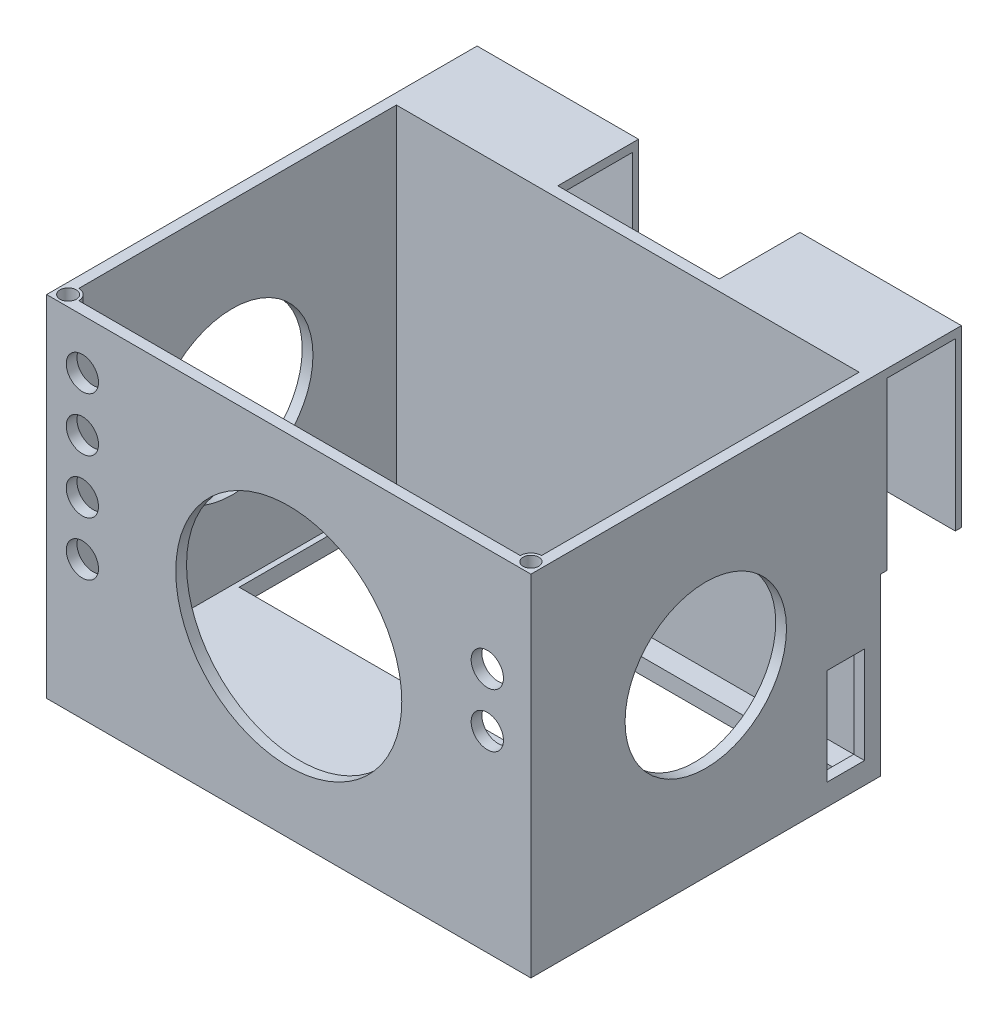
SolidWorks part; units mm, degrees
ref_plane "Front Plane" through (0, 0, 0) normal (0, 0, 1) x (1, 0, 0)
ref_plane "Top Plane" through (0, 0, 0) normal (0, 1, 0) x (1, 0, 0)
ref_plane "Right Plane" through (0, 0, 0) normal (1, 0, 0) x (0, 0, -1)
sketch "Sketch7" plane through (0, 0, 0) normal (0, 1, 0) x (1, 0, 0)
  line L1 (-45, 32.5) -> (45, 32.5)
  line L2 (-45, 32.5) -> (-45, -32.5)
  line L3 (-45, -32.5) -> (45, -32.5)
  line L4 (45, 32.5) -> (45, -32.5)
  line L5 (-45, 32.5) -> (45, -32.5) construction
  line L6 (-45, -32.5) -> (45, 32.5) construction
  line L11 (-42.1497, 30.4415) -> (26.6705, -19.262) construction
  point P0 (0, 0)
  point P6 (0, 0)
  dimension "D1" = 90
  dimension "D2" = 65
extrude "Boss-Extrude2" add sketch "Sketch7" against normal blind 65
sketch "Sketch10" plane through (0, 0, 0) normal (0, 1, 0) x (1, 0, 0)
  line L1 (-43, 30.5) -> (43, 30.5)
  line L2 (-43, 30.5) -> (-43, -30.5)
  line L3 (-43, -30.5) -> (43, -30.5)
  line L4 (43, 30.5) -> (43, -30.5)
  line L5 (-43, 30.5) -> (43, -30.5) construction
  line L6 (-43, -30.5) -> (43, 30.5) construction
  point P0 (0, 0)
  dimension "D1" = 86
  dimension "D2" = 61
extrude "Cut-Extrude2" cut sketch "Sketch10" against normal blind 62
sketch "Sketch12" plane through (-45, 0, 0) normal (-1, 0, 0) x (0, 0, 1)
  circle A0 centre (0, -32.5) radius 15
extrude "Cut-Extrude3" cut sketch "Sketch12" against normal through all
sketch "Sketch13" plane through (0, 0, 32.5) normal (0, 0, 1) x (1, 0, 0)
  circle A0 centre (0, -32.5) radius 21
  circle A1 centre (-38.3562, -9.3091) radius 3
  circle A2 centre (-38.3562, -19.3091) radius 3
  circle A3 centre (-38.3562, -29.3091) radius 3
  circle A4 centre (-38.3562, -39.3091) radius 3
  circle A5 centre (36.897, -19.3091) radius 3
  circle A6 centre (36.897, -29.3091) radius 3
  dimension "D1" = 4
  dimension "D2" = 2
extrude "Cut-Extrude4" cut sketch "Sketch13" against normal up to surface (2 mm away) up to face at (0, -31, 30.5)
sketch "Sketch14" plane through (45, 0, 0) normal (1, 0, 0) x (0, 0, -1)
  line L0 (32.5, -65) -> (32.5, 0) construction
  line L3 (29.5, -61) -> (29.5, -43.0371)
  line L4 (29.5, -43.0371) -> (22.5, -43.0371)
  line L5 (22.5, -43.0371) -> (22.5, -61)
  line L6 (22.5, -61) -> (29.5, -61)
  dimension "D1" = 7
  dimension "D2" = 3
extrude "Cut-Extrude5" cut sketch "Sketch14" against normal blind 5
sketch "Sketch15" plane through (0, -65, 0) normal (0, -1, 0) x (1, 0, 0)
  line L0 (-45, -32.5) -> (-45, 32.5) construction
  line L1 (-42, -0.2844) -> (42, -0.2844)
  line L2 (-42, -0.2844) -> (-42, -26.5)
  line L3 (-42, -26.5) -> (42, -26.5)
  line L4 (42, -0.2844) -> (42, -26.5)
  line L5 (45, 32.5) -> (45, -32.5) construction
  line L6 (45, -32.5) -> (-45, -32.5) construction
  dimension "D1" = 3
  dimension "D2" = 3
  dimension "D3" = 6
extrude "Cut-Extrude6" cut sketch "Sketch15" against normal blind 5
sketch "Sketch17" plane through (0, 0, -32.5) normal (0, 0, -1) x (-1, 0, 0)
  line L1 (-45, 0) -> (-15, 0)
  line L2 (-45, 0) -> (-45, -32.5)
  line L3 (-45, -32.5) -> (-15, -32.5)
  line L4 (-15, 0) -> (-15, -32.5)
  line L5 (45, 0) -> (15, 0)
  line L6 (45, 0) -> (45, -32.5)
  line L7 (45, -32.5) -> (15, -32.5)
  line L8 (15, 0) -> (15, -32.5)
  dimension "D1" = 32.5
  dimension "D2" = 30
  dimension "D3" = 30
extrude "Boss-Extrude3" add sketch "Sketch17" along normal blind 15
sketch "Sketch18" plane through (45, 0, 0) normal (1, 0, 0) x (0, 0, -1)
  line L0 (46.367, -32.5) -> (46.367, -1.5517)
  line L1 (47.5, -32.5) -> (32.5, -32.5) construction
  line L2 (46.367, -1.5517) -> (33.6406, -1.5517)
  line L3 (33.6406, -1.5517) -> (33.6406, -32.5)
  line L4 (33.6406, -32.5) -> (46.367, -32.5)
extrude "Cut-Extrude7" cut sketch "Sketch18" against normal through all
sketch "Sketch20" plane through (0, 0, -32.5) normal (0, 0, -1) x (-1, 0, 0)
  line L0 (-12.1406, -53.9179) -> (12.1406, -53.9179)
  line L1 (-12.1406, -13.9179) -> (12.1406, -13.9179)
  line L2 (-12.1406, -13.9179) -> (-12.1406, -20.6391)
  line L3 (-12.1406, -20.6391) -> (12.1406, -20.6391)
  line L4 (12.1406, -13.9179) -> (12.1406, -20.6391)
  line L5 (-12.1406, -13.9179) -> (12.1406, -20.6391) construction
  line L6 (-12.1406, -20.6391) -> (12.1406, -13.9179) construction
  line L7 (-12.1406, -53.9179) -> (-12.1406, -60.6391)
  line L8 (-12.1406, -60.6391) -> (12.1406, -60.6391)
  line L9 (12.1406, -53.9179) -> (12.1406, -60.6391)
  line L10 (-12.1406, -53.9179) -> (12.1406, -60.6391) construction
  line L11 (-12.1406, -60.6391) -> (12.1406, -53.9179) construction
  point P0 (0, -17.2785)
  point P7 (0, -57.2785)
  dimension "D1" = 2
extrude "Boss-Extrude4" add sketch "Sketch20" along normal blind 10
sketch "Sketch21" plane through (0, -13.9179, 0) normal (0, 1, 0) x (1, 0, 0)
  line L1 (-10.7252, 40.7651) -> (10.5834, 40.7651)
  line L2 (-10.7252, 40.7651) -> (-10.7252, 34.237)
  line L3 (-10.7252, 34.237) -> (10.5834, 34.237)
  line L4 (10.5834, 40.7651) -> (10.5834, 34.237)
extrude "Cut-Extrude9" cut sketch "Sketch21" against normal through all
sketch "Sketch23" plane through (0, 0, 0) normal (0, 1, 0) x (1, 0, 0)
  line L0 (43, -30.5) -> (43, 30.5) construction
  line L1 (-43, -30.5) -> (43, -30.5) construction
  line L2 (43, -28.5211) -> (43, -30.5)
  line L5 (43, -30.5) -> (41.0211, -30.5)
  line L6 (-43, -28.5211) -> (-43, -30.5)
  line L7 (-43, -30.5) -> (-41.0211, -30.5)
  arc A0 (43, -28.5211) -> (41.0211, -30.5) centre (43, -30.5) ccw
  arc A1 (-43, -28.5211) -> (-41.0211, -30.5) centre (-43, -30.5) cw
extrude "Boss-Extrude5" add sketch "Sketch23" against normal blind 5
sketch "Sketch24" plane through (0, 0, 0) normal (0, 1, 0) x (1, 0, 0)
  circle A0 centre (-43, -30.5) radius 1.5161
  circle A1 centre (43, -30.5) radius 1.4679
extrude "Cut-Extrude10" cut sketch "Sketch24" against normal blind 3
sketch "Sketch25" plane through (0, -65, 0) normal (0, -1, 0) x (1, 0, 0)
  line L0 (-42, -26.5) -> (42, -26.5) construction
  circle A0 centre (0, -28.5) radius 2.5
  point P4 (0, -26.5)
  dimension "D2" = 5
  dimension "D1" = 2
extrude "Cut-Extrude11" cut sketch "Sketch25" against normal blind 1
